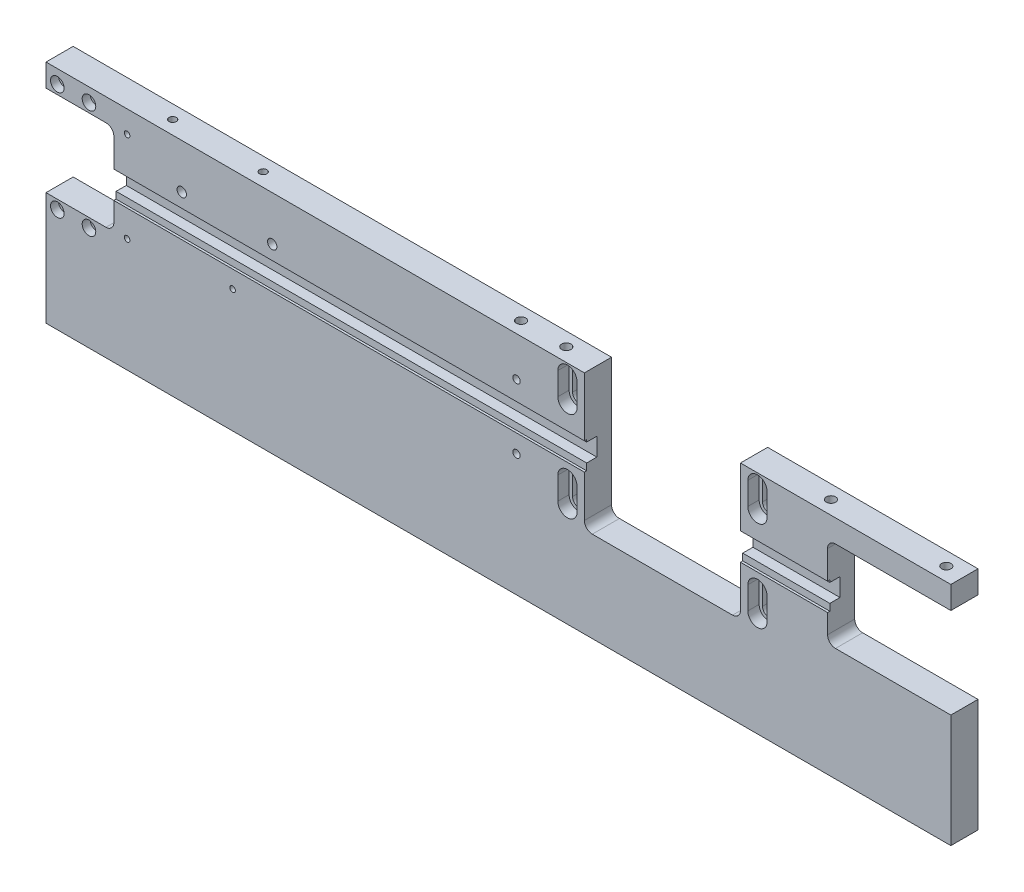
SolidWorks part; units mm, degrees
ref_plane "Front Plane" through (0, 0, 0) normal (0, 0, 1) x (1, 0, 0)
ref_plane "Top Plane" through (0, 0, 0) normal (0, 1, 0) x (1, 0, 0)
ref_plane "Right Plane" through (0, 0, 0) normal (1, 0, 0) x (0, 0, -1)
sketch "Sketch1" plane through (0, 0, 0) normal (0, 0, 1) x (1, 0, 0)
  line L1 (-200, -50) -> (200, -50)
  line L2 (-200, -50) -> (-200, 50)
  line L3 (-200, 50) -> (200, 50)
  line L4 (200, -50) -> (200, 50)
  line L5 (-200, -50) -> (200, 50) construction
  line L6 (-200, 50) -> (200, -50) construction
  point P0 (0, 0)
  dimension "D1" = 400
  dimension "D2" = 100
extrude "Base" add sketch "Sketch1" along normal blind 12
sketch "Sketch2" plane through (0, 0, 12) normal (0, 0, 1) x (1, 0, 0)
  line L0 (200, -50) -> (200, 50) construction
  line L1 (200, 0) -> (149, 0)
  line L2 (200, 0) -> (200, 40)
  line L3 (200, 40) -> (149, 40)
  line L4 (145.5, 3.5) -> (145.5, 36.5)
  line L5 (200, 50) -> (-200, 50) construction
  arc A0 (149, 0) -> (145.5, 3.5) centre (149, 3.5) cw
  arc A1 (149, 40) -> (145.5, 36.5) centre (149, 36.5) ccw
  dimension "D1" = 3.5
  dimension "D2" = 3.5
  dimension "D3" = 40
  dimension "D4" = 51
  dimension "D5" = 33
  dimension "D6" = 10
extrude "Part Tape Mover Cutout" cut sketch "Sketch2" against normal through all
sketch "Sketch3" plane through (0, 0, 12) normal (0, 0, 1) x (1, 0, 0)
  line L0 (200, 50) -> (-200, 50) construction
  line L1 (41.5, -10) -> (103.5, -10)
  line L2 (38, -6.5) -> (38, 50)
  line L3 (38, 50) -> (107, 50)
  line L4 (107, -6.5) -> (107, 50)
  line L5 (-200, -50) -> (200, -50) construction
  line L6 (200, -50) -> (200, 0) construction
  arc A0 (103.5, -10) -> (107, -6.5) centre (103.5, -6.5) ccw
  arc A1 (41.5, -10) -> (38, -6.5) centre (41.5, -6.5) cw
  point P9 (107, -10)
  point P12 (38, -10)
  dimension "D3" = 3.5
  dimension "D4" = 3.5
  dimension "D1" = 69
  dimension "D2" = 60
  dimension "D5" = 40
  dimension "D6" = 93
extrude "Press Plate Cutout" cut sketch "Sketch3" against normal through all
sketch "Sketch4" plane through (0, 0, 12) normal (0, 0, 1) x (1, 0, 0)
  line L0 (-200, 50) -> (-200, -50) construction
  line L1 (-200, 40) -> (-173.5, 40)
  line L2 (-200, 40) -> (-200, 0)
  line L3 (-200, 0) -> (-173.5, 0)
  line L4 (-170, 36.5) -> (-170, 3.5)
  line L5 (38, 50) -> (-200, 50) construction
  arc A0 (-173.5, 0) -> (-170, 3.5) centre (-173.5, 3.5) ccw
  arc A1 (-173.5, 40) -> (-170, 36.5) centre (-173.5, 36.5) cw
  dimension "D1" = 3.5
  dimension "D2" = 3.5
  dimension "D3" = 40
  dimension "D4" = 10
  dimension "D5" = 26.5
extrude "Roller Cutout" cut sketch "Sketch4" against normal through all
sketch "Sketch5" plane through (0, 0, 12) normal (0, 0, 1) x (1, 0, 0)
  line L0 (-170, 3.5) -> (-170, 36.5) construction
  line L1 (-170, 23) -> (145.5, 23)
  line L2 (-170, 23) -> (-170, 15)
  line L3 (-170, 15) -> (145.5, 15)
  line L4 (145.5, 23) -> (145.5, 15)
  line L5 (145.5, 36.5) -> (145.5, 3.5) construction
  line L6 (38, 50) -> (-200, 50) construction
  dimension "D1" = 8
  dimension "D2" = 27
extrude "Part Tape Cutout" cut sketch "Sketch5" against normal blind 5.5
sketch "Sketch6" plane through (0, 0, 12) normal (0, 0, 1) x (1, 0, 0)
  line L1 (-170, 24) -> (145.5, 24)
  line L2 (-170, 24) -> (-170, 12)
  line L3 (-170, 12) -> (145.5, 12)
  line L4 (145.5, 24) -> (145.5, 12)
  line L8 (-170, 3.5) -> (-170, 15) construction
  line L10 (-170, 15) -> (38, 15) construction
  line L11 (145.5, 15) -> (145.5, 3.5) construction
  dimension "D1" = 12
  dimension "D2" = 3
extrude "Cut-Extrude5" cut sketch "Sketch6" against normal blind 1
sketch "Sketch7" plane through (0, 0, 12) normal (0, 0, 1) x (1, 0, 0)
  line L0 (-200, -50) -> (200, -50) construction
  line L1 (200, -50) -> (200, 0) construction
  circle A0 centre (190, -40) radius 6
  circle A1 centre (-50, -40) radius 6
  circle A2 centre (-50, 40) radius 6
  dimension "D1" = 12
  dimension "D2" = 10
  dimension "D3" = 10
  dimension "D4" = 240
  dimension "D5" = 80
extrude "Cut-Extrude6" [suppressed] cut sketch "Sketch7" against normal blind 6.5
sketch "Sketch8" [suppressed] plane through (0, 0, 5.5) normal (0, 0, 1) x (1, 0, 0)
  circle A0 centre (190, -40) radius 3.25
  circle A1 centre (-50, -40) radius 3.25
  circle A2 centre (-50, 40) radius 3.25
  dimension "D1" = 6.5
extrude "Cut-Extrude7" [suppressed] cut sketch "Sketch8" against normal through all
sketch "Sketch9" plane through (0, 50, 0) normal (0, 1, 0) x (1, 0, 0)
  line L1 (200, -12) -> (200, 0) construction
  circle A0 centre (141, -6) radius 2.065
  circle A1 centre (192, -6) radius 2.065
  point P6 (200, -6)
  dimension "D1" = 4.13
  dimension "D2" = 51
  dimension "D3" = 8
extrude "Cut-Extrude8" cut sketch "Sketch9" against normal blind 10
sketch "Sketch11" plane through (0, 0, 12) normal (0, 0, 1) x (1, 0, 0)
  line L0 (114.5, 35) -> (114.5, 45) construction
  line L1 (110.25, 35) -> (110.25, 45)
  line L2 (118.75, 35) -> (118.75, 45)
  line L4 (107, 24) -> (107, 50) construction
  line L5 (200, 50) -> (107, 50) construction
  arc A0 (110.25, 35) -> (118.75, 35) centre (114.5, 35) ccw
  arc A1 (118.75, 45) -> (110.25, 45) centre (114.5, 45) ccw
  point P2 (114.5, 40)
  dimension "D1" = 4.25
  dimension "D4" = 5
  dimension "D2" = 10
  dimension "D3" = 3.25
extrude "Cut-Extrude9" cut sketch "Sketch11" against normal blind 5
sketch "Sketch12" plane through (0, 0, 7) normal (0, 0, 1) x (1, 0, 0)
  line L4 (117.25, 35) -> (117.25, 45)
  line L5 (111.75, 45) -> (111.75, 35)
  line L6 (117.25, 35) -> (117.25, 45)
  line L7 (111.75, 45) -> (111.75, 35)
  arc A4 (111.75, 35) -> (117.25, 35) centre (114.5, 35) ccw
  arc A5 (117.25, 45) -> (111.75, 45) centre (114.5, 45) ccw
  arc A6 (111.75, 35) -> (117.25, 35) centre (114.5, 35) ccw
  arc A7 (117.25, 45) -> (111.75, 45) centre (114.5, 45) ccw
  dimension "D1" = 1.5
extrude "Cut-Extrude10" cut sketch "Sketch12" against normal through all
pattern_linear "LPattern1" count 2 spacing 84 along (-1, 0, 0) count 2 spacing 40 along (0, -1, 0) of "Cut-Extrude9", "Cut-Extrude10"
sketch "Sketch13" plane through (0, 0, 12) normal (0, 0, 1) x (1, 0, 0)
  line L0 (-173.5, 40) -> (-200, 40) construction
  line L1 (-200, 50) -> (-200, 40) construction
  circle A0 centre (-181, 44) radius 3
  circle A1 centre (-195, 44) radius 3
  dimension "D1" = 6
  dimension "D3" = 5
  dimension "D2" = 14
  dimension "D4" = 4
extrude "Cut-Extrude11" cut sketch "Sketch13" against normal blind 3.5
sketch "Sketch14" plane through (0, 0, 8.5) normal (0, 0, 1) x (1, 0, 0)
  circle A0 centre (-181, 44) radius 1.5
  circle A1 centre (-195, 44) radius 1.5
  dimension "D1" = 3
extrude "Cut-Extrude12" cut sketch "Sketch14" against normal through all
pattern_linear "LPattern2" count 2 spacing 48 along (0, -1, 0) of "Cut-Extrude11", "Cut-Extrude12"
sketch "Sketch15" plane through (0, 0, 12) normal (0, 0, 1) x (1, 0, 0)
  line L0 (38, 24) -> (-170, 24) construction
  line L1 (-170, 12) -> (38, 12) construction
  line L2 (-170, 24) -> (-170, 36.5) construction
  line L3 (-170, 3.5) -> (-170, 12) construction
  circle A0 centre (-164.15, 40.25) radius 1.23
  circle A1 centre (-164.15, 0.25) radius 1.23
  circle A2 centre (-117.5, 4.3) radius 1.23
  dimension "D2" = 2.46
  dimension "D3" = 5.85
  dimension "D5" = 7.7
  dimension "D1" = 16.25
  dimension "D4" = 40
  dimension "D6" = 52.5
extrude "Cut-Extrude13" cut sketch "Sketch15" against normal through all
sketch "Sketch16" plane through (0, 0, 12) normal (0, 0, 1) x (1, 0, 0)
  line L0 (38, 24) -> (-170, 24) construction
  line L1 (-170, 24) -> (-170, 36.5) construction
  circle A0 centre (-140, 30.25) radius 2.065
  circle A1 centre (-100, 30.25) radius 2.065
  dimension "D1" = 4.13
  dimension "D2" = 40
  dimension "D3" = 6.25
  dimension "D4" = 30
extrude "Cut-Extrude14" cut sketch "Sketch16" against normal through all
sketch "Sketch18" plane through (0, 0, 12) normal (0, 0, 1) x (1, 0, 0)
  line L0 (38, 50) -> (-200, 50) construction
  line L1 (38, 50) -> (38, 24) construction
  circle A0 centre (8, 32.5) radius 1.62
  circle A1 centre (8, 4) radius 1.62
  dimension "D1" = 3.24
  dimension "D3" = 17.5
  dimension "D4" = 30
  dimension "D2" = 28.5
extrude "Cut-Extrude15" cut sketch "Sketch18" against normal through all
sketch "Sketch19" plane through (0, 50, 0) normal (0, 1, 0) x (1, 0, 0)
  line L2 (38, 0) -> (38, -12) construction
  line L3 (-200, -12) -> (-200, 0) construction
  circle A0 centre (24, -6) radius 2.065
  circle A1 centre (4, -6) radius 2.065
  circle A2 centre (-110, -6) radius 1.62
  circle A3 centre (-150, -6) radius 1.62
  point P14 (38, -6)
  dimension "D1" = 4.13
  dimension "D2" = 20
  dimension "D3" = 14
  dimension "D4" = 3.24
  dimension "D5" = 40
  dimension "D6" = 50
extrude "Cut-Extrude16" cut sketch "Sketch19" against normal blind 8
